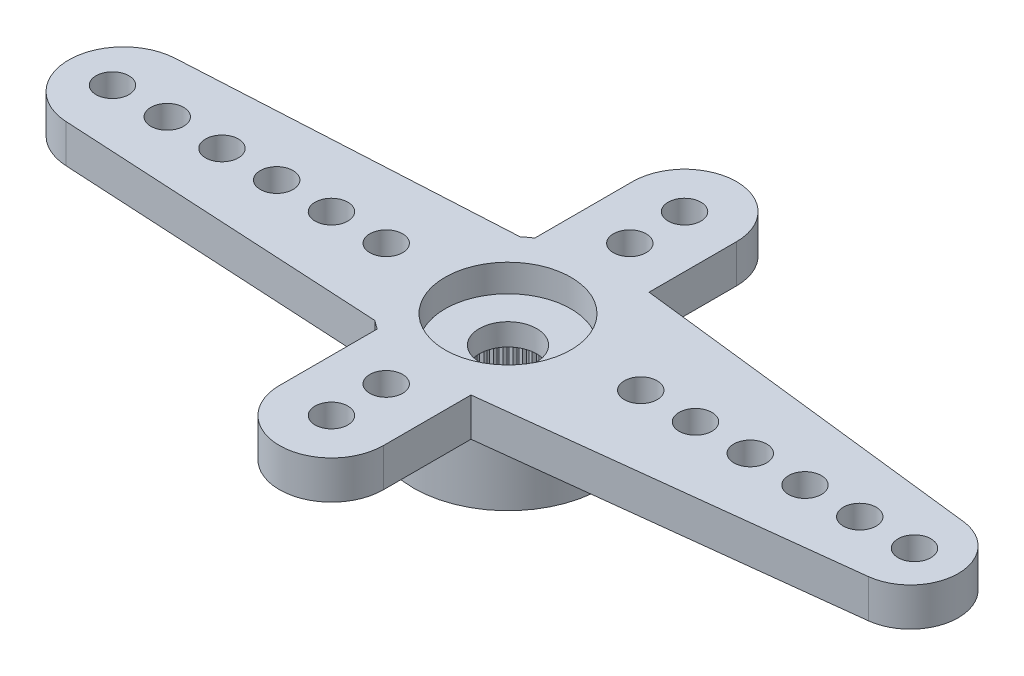
SolidWorks part; units mm, degrees
material "PVC Rígido"
ref_plane "Plano frontal" through (0, 0, 0) normal (0, 0, 1) x (1, 0, 0)
ref_plane "Plano superior" through (0, 0, 0) normal (0, 1, 0) x (1, 0, 0)
ref_plane "Plano direito" through (0, 0, 0) normal (1, 0, 0) x (0, 0, -1)
sketch "Esboço1" plane through (0, 0, 0) normal (0, 1, 0) x (1, 0, 0)
  line L0 (0, 0) -> (-14.05, 0) construction
  line L1 (-14.1591, 1.997) -> (-2.2091, 2.65)
  line L2 (-2.2091, -2.65) -> (-14.1591, -1.997)
  arc A0 (-2.2091, -2.65) -> (-2.2091, 2.65) centre (0, 0) ccw
  arc A1 (-14.1591, 1.997) -> (-14.1591, -1.997) centre (-14.05, 0) ccw
  dimension "D1" = 6.9
  dimension "D2" = 4
  dimension "D3" = 19.5
  dimension "D4" = 5.3
extrude "Ressalto-extrusão1" add sketch "Esboço1" against normal blind 1.4
sketch "Esboço2" plane through (0, -1.4, 0) normal (0, -1, 0) x (1, 0, 0)
  arc A0 (-2.2091, -2.65) -> (-2.2091, 2.65) centre (0, 0) ccw construction
  circle A1 centre (0, 0) radius 3.45
extrude "Ressalto-extrusão2" add sketch "Esboço2" along normal offset from surface (2.4 mm away) 3.8 up to face at (-7.242, 0, 0)
hole_wizard "Furo1" positions "Esboço9" profile "Esboço10" legacy end condition through all
sketch "Esboço9" plane through (0, 0, 0) normal (0, 1, 0) x (1, 0, 0)
  line L1 (-14.45, 0) -> (0, 0) construction
  arc A2 (-14.1591, 1.997) -> (-14.1591, -1.997) centre (-14.05, 0) ccw construction
  point P0 (-14.45, 0)
  point P19 (-16.05, 0)
  dimension "D1" = 1.6
sketch "Esboço10" plane through (-14.45, 0, 0) normal (1, 0, 0) x (0, 0, 1)
  line L0 (0, 0) -> (0, 3.8)
  line L1 (0, 3.8) -> (0.6, 3.8)
  line L2 (0.6, 3.8) -> (0.6, 0)
  line L3 (0.6, 0) -> (0, 0)
  line L4 (0, 110) -> (0, -10) construction
  dimension "Diameter" = 1.2
  dimension "Depth" = 3.8
pattern_linear "Padrão linear1" count 6 spacing 2 along (1, 0, 0) of "Furo1"
sketch "Esboço12" plane through (0, 0, 0) normal (0, 1, 0) x (1, 0, 0)
  line L0 (0.399, 3.4269) -> (14.9024, 1.7383)
  line L1 (14.9024, -1.7383) -> (0.399, -3.4269)
  arc A0 (-2.2091, -2.65) -> (-2.2091, 2.65) centre (0, 0) ccw construction
  arc A1 (0.399, -3.4269) -> (0.399, 3.4269) centre (0, 0) ccw
  arc A2 (14.9024, 1.7383) -> (14.9024, -1.7383) centre (14.7, 0) cw
  arc A3 (-14.1591, 1.997) -> (-14.1591, -1.997) centre (-14.05, 0) ccw construction
  dimension "D1" = 1.75
  dimension "D2" = 32.5
extrude "Ressalto-extrusão3" add sketch "Esboço12" against normal up to surface (1.4 mm away) up to face at (-12.45, -1.4, 0.6)
hole_wizard "Furo2" positions "Esboço13" profile "Esboço14" legacy end condition through all
sketch "Esboço13" plane through (0, 0, 0) normal (0, 1, 0) x (1, 0, 0)
  line L0 (0, 0) -> (14.85, 0) construction
  arc A0 (14.9024, -1.7383) -> (14.9024, 1.7383) centre (14.7, 0) ccw construction
  point P0 (14.85, 0)
  point P6 (16.45, 0)
  dimension "D1" = 1.6
sketch "Esboço14" plane through (14.85, 0, 0) normal (1, 0, 0) x (0, 0, 1)
  line L0 (0, 0) -> (0, 3.8)
  line L1 (0, 3.8) -> (0.6, 3.8)
  line L2 (0.6, 3.8) -> (0.6, 0)
  line L3 (0.6, 0) -> (0, 0)
  line L4 (0, 110) -> (0, -10) construction
  dimension "Diameter" = 1.2
  dimension "Depth" = 3.8
pattern_linear "Padrão linear2" count 6 spacing 2 along (-1, 0, 0) of "Furo2"
sketch "Esboço16" plane through (0, 0, 0) normal (0, 1, 0) x (1, 0, 0)
  line L0 (0, -6.45) -> (0, 6.45) construction
  line L1 (-1.9, -6.45) -> (-1.9, 6.45)
  line L2 (1.9, -6.45) -> (1.9, 6.45)
  arc A0 (-1.9, -6.45) -> (1.9, -6.45) centre (0, -6.45) ccw
  arc A1 (1.9, 6.45) -> (-1.9, 6.45) centre (0, 6.45) ccw
  point P2 (0, 0)
  dimension "D2" = 16.7
  dimension "D1" = 3.8
extrude "Ressalto-extrusão4" add sketch "Esboço16" against normal up to surface (1.4 mm away) up to face at (12.85, -1.4, 0.6)
hole_wizard "Furo3" positions "Esboço17" profile "Esboço18" legacy end condition through all
sketch "Esboço17" plane through (0, 0, 0) normal (0, 1, 0) x (1, 0, 0)
  point P0 (0, -6.45)
sketch "Esboço18" plane through (0, 0, 6.45) normal (1, 0, 0) x (0, 0, 1)
  line L0 (0, 0) -> (0, 3.8)
  line L1 (0, 3.8) -> (0.6, 3.8)
  line L2 (0.6, 3.8) -> (0.6, 0)
  line L3 (0.6, 0) -> (0, 0)
  line L4 (0, 110) -> (0, -10) construction
  dimension "Diameter" = 1.2
  dimension "Depth" = 3.8
pattern_linear "Padrão linear3" count 2 spacing 2 along (0, 0, -1) of "Furo3"
pattern_circular "PadrãoCircular1" count 2 over 360 about axis through (0, 0, 0) along (0, 1, 0) of "Padrão linear3", "Furo3"
hole_wizard "Furo4" positions "Esboço3" profile "Esboço4" legacy
sketch "Esboço3" plane through (0, -3.8, 0) normal (0, -1, 0) x (-1, 0, 0)
  point P0 (0, 0)
sketch "Esboço4" plane through (0, -3.8, 0) normal (1, 0, 0) x (0, 0, -1)
  line L0 (0, 0) -> (0, 2)
  line L1 (0, 2) -> (2.475, 2)
  line L2 (2.475, 2) -> (2.475, 0)
  line L3 (2.475, 0) -> (0, 0)
  line L4 (0, 110) -> (0, -10) construction
  dimension "Diameter" = 4.95
  dimension "Depth" = 2
hole_wizard "Furo5" positions "Esboço5" profile "Esboço6" legacy
sketch "Esboço5" plane through (0, 0, 0) normal (0, 1, 0) x (1, 0, 0)
  point P0 (0, 0)
sketch "Esboço6" plane through (0, 0, 0) normal (1, 0, 0) x (0, 0, 1)
  line L0 (0, 0) -> (0, 1)
  line L1 (0, 1) -> (2.3, 1)
  line L2 (2.3, 1) -> (2.3, 0)
  line L3 (2.3, 0) -> (0, 0)
  line L4 (0, 110) -> (0, -10) construction
  dimension "Diameter" = 4.6
  dimension "Depth" = 1
hole_wizard "Furo6" positions "Esboço7" profile "Esboço8" legacy end condition through all
sketch "Esboço7" plane through (0, 0, 0) normal (0, 1, 0) x (1, 0, 0)
  point P0 (0, 0)
sketch "Esboço8" plane through (0, 0, 0) normal (1, 0, 0) x (0, 0, 1)
  line L0 (0, 0) -> (0, 3.8)
  line L1 (0, 3.8) -> (1.05, 3.8)
  line L2 (1.05, 3.8) -> (1.05, 0)
  line L3 (1.05, 0) -> (0, 0)
  line L4 (0, 110) -> (0, -10) construction
  dimension "Diameter" = 2.1
  dimension "Depth" = 3.8
sketch "Esboço11" plane through (0, -3.8, 0) normal (0, -1, 0) x (1, 0, 0)
  line L0 (-0.0981, 2.4731) -> (0, 2.375)
  line L1 (0, 2.375) -> (0.0981, 2.4731)
  line L2 (0, 0) -> (0, 2.475) construction
  circle A0 centre (0, 0) radius 2.375 construction
  circle A1 centre (0, 0) radius 2.475
  arc A2 (0.0981, 2.4731) -> (-0.0981, 2.4731) centre (0, 0) ccw
  dimension "D3" = 4.75
  dimension "D2" = 0.1
  dimension "D1" = 0
extrude "Ressalto-extrusão5" add sketch "Esboço11" against normal up to surface (2 mm away) up to face at (0, -1.8, 1.05)
pattern_circular "PadrãoCircular2" count 60 over 360 about axis through (0, 0, 0) along (0, 1, 0) of "Ressalto-extrusão5"
